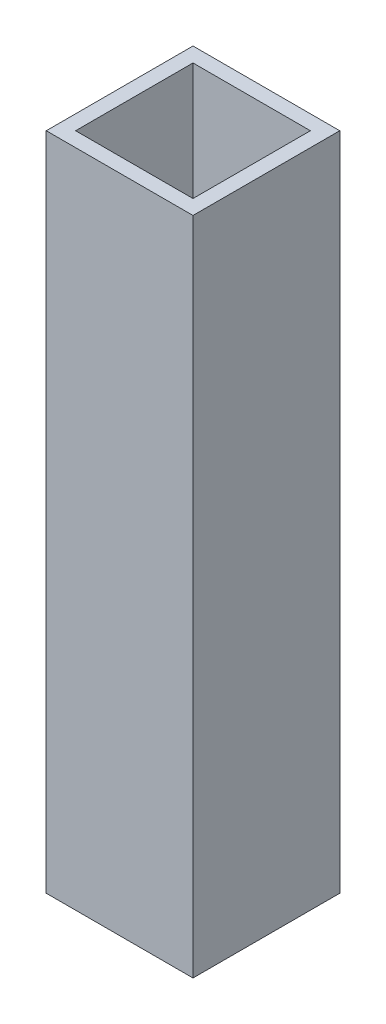
SolidWorks part; units mm, degrees
ref_plane "Front Plane" through (0, 0, 0) normal (0, 0, 1) x (1, 0, 0)
ref_plane "Top Plane" through (0, 0, 0) normal (0, 1, 0) x (1, 0, 0)
ref_plane "Right Plane" through (0, 0, 0) normal (1, 0, 0) x (0, 0, -1)
sketch "Sketch1" plane through (0, 0, 0) normal (0, 1, 0) x (1, 0, 0)
  line L0 (-10.16, 10.16) -> (10.16, 10.16)
  line L1 (-12.7, 12.7) -> (12.7, 12.7)
  line L2 (-12.7, 12.7) -> (-12.7, -12.7)
  line L3 (-12.7, -12.7) -> (12.7, -12.7)
  line L4 (12.7, 12.7) -> (12.7, -12.7)
  line L5 (-12.7, 12.7) -> (12.7, -12.7) construction
  line L6 (-12.7, -12.7) -> (12.7, 12.7) construction
  line L7 (10.16, 10.16) -> (10.16, -10.16)
  line L8 (-10.16, -10.16) -> (10.16, -10.16)
  line L9 (-10.16, 10.16) -> (-10.16, -10.16)
  point P0 (0, 0)
  dimension "D1" = 25.4
  dimension "D2" = 25.4
  dimension "D3" = 2.54
extrude "Boss-Extrude1" add sketch "Sketch1" along normal blind 114.3
